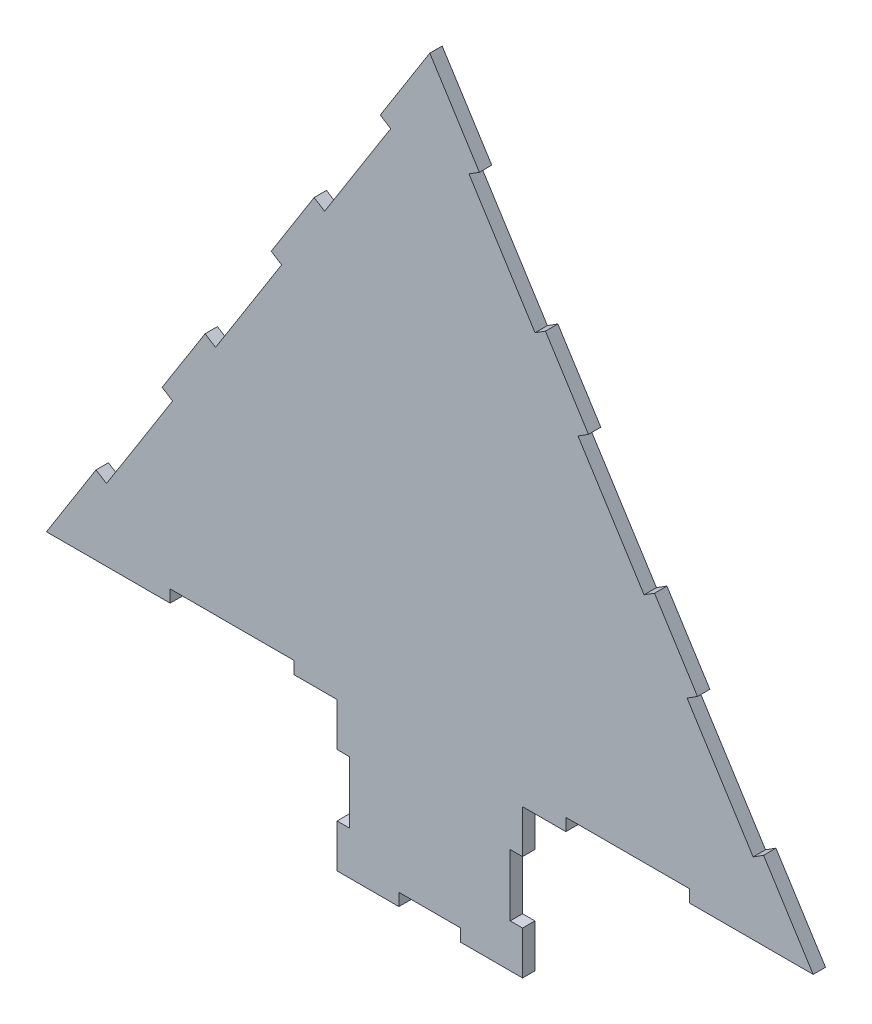
SolidWorks part; units mm, degrees
ref_plane "Plan de face" through (0, 0, 0) normal (0, 0, 1) x (1, 0, 0)
ref_plane "Plan de dessus" through (0, 0, 0) normal (0, 1, 0) x (1, 0, 0)
ref_plane "Plan de droite" through (0, 0, 0) normal (1, 0, 0) x (0, 0, -1)
sketch "Esquisse1" plane through (0, 0, 0) normal (0, 0, 1) x (1, 0, 0)
  line L1 (-310, 0) -> (0, 490.204)
  line L2 (0, 490.204) -> (310, 0)
  line L3 (-310, 0) -> (-75, 0)
  line L5 (-75, 0) -> (-75, -120)
  line L6 (-75, -120) -> (75, -120)
  line L7 (75, 0) -> (75, -120)
  line L8 (75, 0) -> (310, 0)
  point P4 (0, 0)
  dimension "D1" = 620
  dimension "D2" = 580
  dimension "D3" = 580
  dimension "D4" = 150
  dimension "D5" = 120
  dimension "D6" = 310
  dimension "D7" = 310
  dimension "D8" = 75
extrude "Boss.-Extru.1" add sketch "Esquisse1" along normal blind 10
sketch "Esquisse2" plane through (0, 0, 10) normal (0, 0, 1) x (1, 0, 0)
  line L5 (-269.9138, 63.3885) -> (-261.462, 58.0436)
  line L14 (0, 490.204) -> (-310, 0) construction
  line L15 (-261.462, 58.0436) -> (-208.0137, 142.5616)
  line L16 (-208.0137, 142.5616) -> (-216.4655, 147.9064)
  line L17 (-216.4655, 147.9064) -> (-269.9138, 63.3885)
  line L18 (-181.7241, 202.8431) -> (-173.2723, 197.4982)
  line L19 (-173.2723, 197.4982) -> (-119.8241, 282.0162)
  line L20 (-119.8241, 282.0162) -> (-128.2759, 287.361)
  line L21 (-128.2759, 287.361) -> (-181.7241, 202.8431)
  line L22 (-93.5345, 342.2976) -> (-85.0827, 336.9528)
  line L23 (-85.0827, 336.9528) -> (-31.6344, 421.4708)
  line L24 (-31.6344, 421.4708) -> (-40.0862, 426.8156)
  line L25 (-40.0862, 426.8156) -> (-93.5345, 342.2976)
  line L26 (0, 0) -> (0, 490.204) construction
  line L27 (208.0137, 142.5616) -> (216.4655, 147.9064)
  line L28 (261.462, 58.0436) -> (208.0137, 142.5616)
  line L29 (269.9138, 63.3885) -> (261.462, 58.0436)
  line L30 (216.4655, 147.9064) -> (269.9138, 63.3885)
  line L31 (31.6344, 421.4708) -> (40.0862, 426.8156)
  line L32 (85.0827, 336.9528) -> (31.6344, 421.4708)
  line L33 (93.5345, 342.2976) -> (85.0827, 336.9528)
  line L34 (40.0862, 426.8156) -> (93.5345, 342.2976)
  line L35 (119.8241, 282.0162) -> (128.2759, 287.361)
  line L36 (173.2723, 197.4982) -> (119.8241, 282.0162)
  line L37 (181.7241, 202.8431) -> (173.2723, 197.4982)
  line L38 (128.2759, 287.361) -> (181.7241, 202.8431)
  line L39 (-310, 0) -> (-75, 0) construction
  line L40 (-210, 0) -> (-110, 0)
  line L41 (-210, 0) -> (-210, 10)
  line L42 (-210, 10) -> (-110, 10)
  line L43 (-110, 0) -> (-110, 10)
  line L44 (210, 10) -> (110, 10)
  line L45 (110, 0) -> (110, 10)
  line L46 (210, 0) -> (110, 0)
  line L47 (210, 0) -> (210, 10)
  line L48 (-75, 0) -> (-75, -120) construction
  line L49 (-75, -35) -> (-65, -35)
  line L50 (-75, -35) -> (-75, -85)
  line L51 (-75, -85) -> (-65, -85)
  line L52 (-65, -35) -> (-65, -85)
  line L53 (75, -120) -> (75, 0) construction
  line L54 (75, -35) -> (65, -35)
  line L55 (75, -35) -> (75, -85)
  line L56 (75, -85) -> (65, -85)
  line L57 (65, -35) -> (65, -85)
  line L58 (-75, -120) -> (75, -120) construction
  line L59 (-25, -120) -> (25, -120)
  line L60 (-25, -120) -> (-25, -110)
  line L61 (-25, -110) -> (25, -110)
  line L62 (25, -120) -> (25, -110)
  dimension "D2" = 75
  dimension "D3" = 100
  dimension "D4" = 10
  dimension "D5" = 100
  dimension "D6" = 50
  dimension "D7" = 50
  dimension "D8" = 50
  dimension "D9" = 25
  dimension "D10" = 100
  dimension "D11" = 100
  dimension "D12" = 100
  dimension "D13" = 10
  dimension "D14" = 10
  dimension "D15" = 10
  dimension "D16" = 75
  dimension "D17" = 10
  dimension "D18" = 65
  dimension "D19" = 10
  dimension "D20" = 10
  dimension "D21" = 35
  dimension "D22" = 35
extrude "Enlèv. mat.-Extru.1" cut sketch "Esquisse2" against normal blind 10
